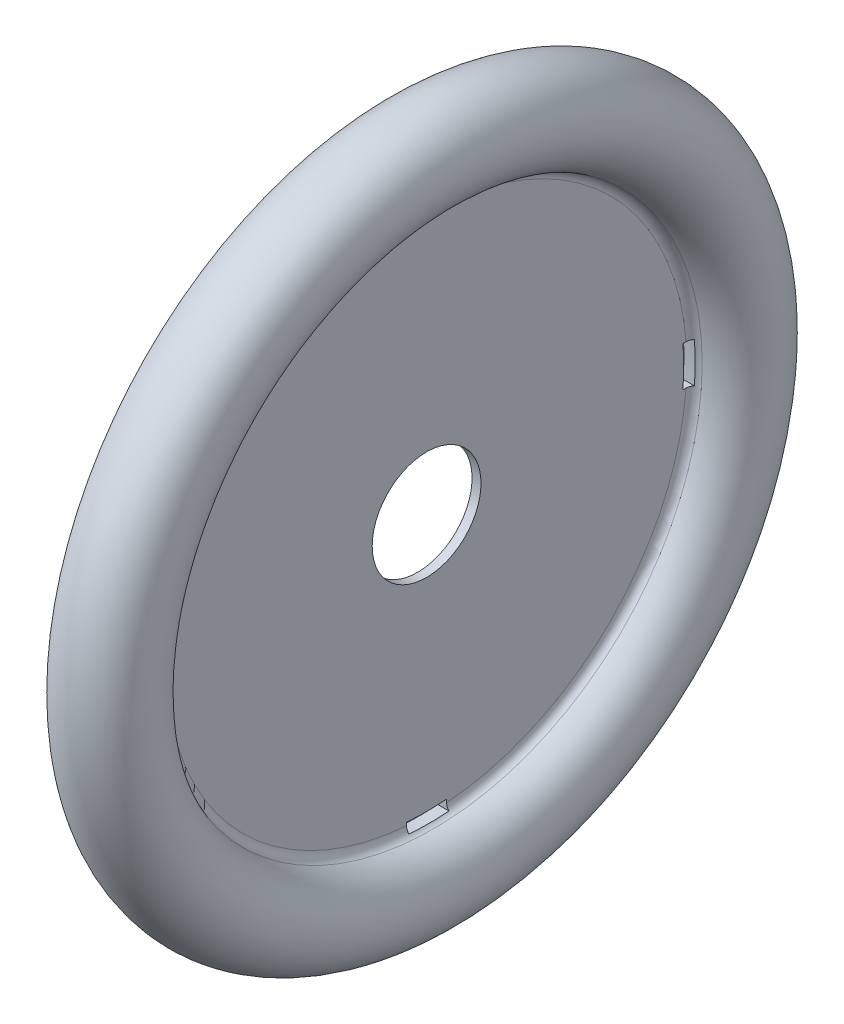
SolidWorks part; units mm, degrees
ref_plane "Front Plane" through (0, 0, 0) normal (0, 0, 1) x (1, 0, 0)
ref_plane "Top Plane" through (0, 0, 0) normal (0, 1, 0) x (1, 0, 0)
ref_plane "Right Plane" through (0, 0, 0) normal (1, 0, 0) x (0, 0, -1)
sketch "Sketch1" plane through (0, 0, 0) normal (0, 0, 1) x (1, 0, 0)
  line L0 (0, 0) -> (24032.2404, 0) construction
  line L1 (0.4064, 23.0883) -> (0.4064, 4.826)
  line L2 (0, 27.6905) -> (0, 31.6529) construction
  line L3 (0, 27.6905) -> (3.9624, 27.6905) construction
  line L4 (-0.3873, 23.749) -> (-0.3874, 4.826)
  line L5 (-0.3874, 4.826) -> (0.4064, 4.826)
  line L6 (-2.214, 29.9573) -> (-2.7686, 30.5252)
  line L7 (-0.3873, 24.5456) -> (-0.3874, 4.826) construction
  line L8 (0.4064, 23.749) -> (0.4064, 4.826) construction
  arc A0 (-2.7686, 30.5252) -> (0.9999, 23.8563) centre (0, 27.6905) cw
  arc A1 (-2.214, 29.9573) -> (0.325, 24.5386) centre (0, 27.6905) cw
  arc A2 (-2.214, 29.9573) -> (-0.3873, 24.5456) centre (0, 27.6905) cw construction
  arc A3 (0.325, 24.5386) -> (-0.3873, 23.749) centre (0.4064, 23.749) ccw
  arc A4 (-2.7686, 30.5252) -> (0.4064, 23.749) centre (0, 27.6905) cw construction
  arc A5 (0.9999, 23.8563) -> (0.4064, 23.0883) centre (1.2002, 23.0883) ccw
  point P9 (0.0095, 4.826)
  point P20 (0.4064, 23.749)
  point P21 (-1.7858, 23.0883)
  point P22 (-4.6364, 23.0883)
  point P23 (0, 0)
  point P24 (0, 0)
  point P25 (0, 0)
  point P26 (0, 27.6905)
  dimension "D2" = 3.9624
  dimension "D7" = 0.7937
  dimension "D1" = 47.498
  dimension "D3" = 6.731
  dimension "D4" = 3.556
  dimension "D6" = 9.652
  dimension "D5" = 0.7937
revolve "Revolve1" add sketch "Sketch1" angle 360 about L0
sketch "Sketch2" plane through (0.4064, 0, 0) normal (1, 0, 0) x (0, 0, -1)
  line L11 (-1.778, 22.7422) -> (-1.778, 23.555)
  line L12 (1.778, 22.7422) -> (1.778, 23.555)
  arc A0 (-1.778, 23.555) -> (1.778, 23.555) centre (0, 0) cw
  arc A1 (-1.778, 22.7422) -> (1.778, 22.7422) centre (0, 0) cw
  point P0 (3.5832, 15.9027)
  point P14 (0, 0)
  point P15 (3.4551, 15.4166)
  point P16 (0, 0)
  dimension "D2" = 23.622
  dimension "D1" = 3.556
  dimension "D3" = 0.8128
extrude "Cut-Extrude1" cut sketch "Sketch2" against normal through all both and the other way through all
pattern_circular "CirPattern1" count 4 over 360 about axis through (0, 0, 0) along (1, 0, 0) of "Cut-Extrude1"
